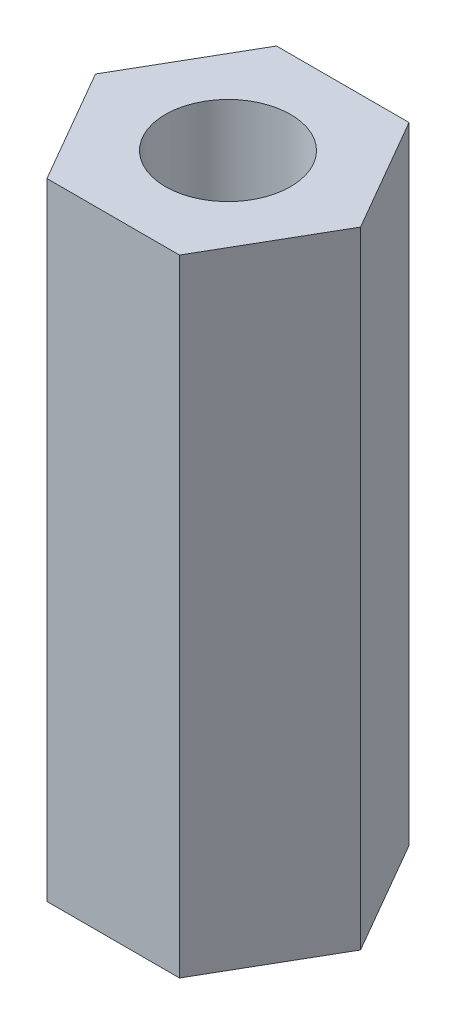
SolidWorks part; units mm, degrees
ref_plane "Front Plane" through (0, 0, 0) normal (0, 0, 1) x (1, 0, 0)
ref_plane "Top Plane" through (0, 0, 0) normal (0, 1, 0) x (1, 0, 0)
ref_plane "Right Plane" through (0, 0, 0) normal (1, 0, 0) x (0, 0, -1)
sketch "Sketch1" plane through (0, 0, 0) normal (0, 1, 0) x (1, 0, 0)
  line L1 (-1.5877, 2.75) -> (-3.1754, 0)
  line L2 (-3.1754, 0) -> (-1.5877, -2.75)
  line L3 (-1.5877, -2.75) -> (1.5877, -2.75)
  line L4 (1.5877, -2.75) -> (3.1754, 0)
  line L5 (3.1754, 0) -> (1.5877, 2.75)
  line L6 (1.5877, 2.75) -> (-1.5877, 2.75)
  circle A0 centre (0, 0) radius 2.75 construction
  circle A1 centre (0, 0) radius 1.5
  dimension "D2" = 3
  dimension "D1" = 5.5
extrude "Boss-Extrude1" add sketch "Sketch1" along normal blind 15
